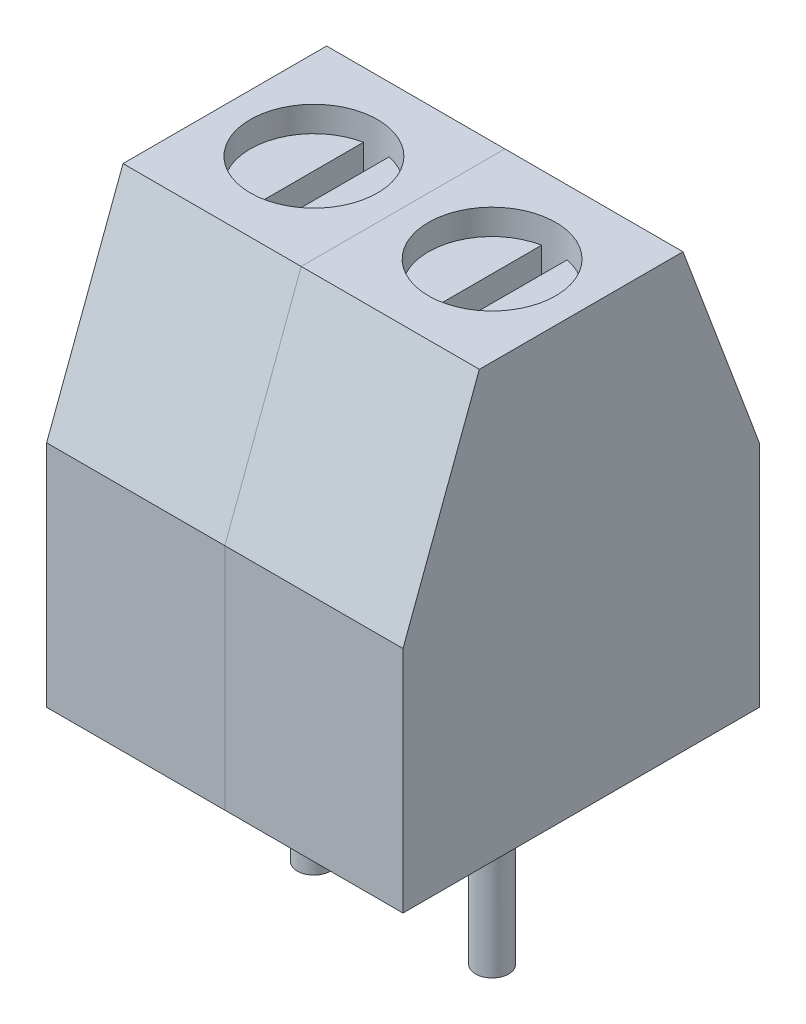
SolidWorks part; units mm, degrees
ref_plane "정면" through (0, 0, 0) normal (0, 0, 1) x (1, 0, 0)
ref_plane "윗면" through (0, 0, 0) normal (0, 1, 0) x (1, 0, 0)
ref_plane "우측면" through (0, 0, 0) normal (1, 0, 0) x (0, 0, -1)
sketch "스케치1" plane through (0, 0, 0) normal (1, 0, 0) x (0, 0, -1)
  line L0 (0, 4.5) -> (0, 8.5) construction
  line L1 (0, 0) -> (7, 0)
  line L2 (0, 0) -> (0, 4.5)
  line L3 (0, 8.5) -> (7, 8.5) construction
  line L4 (7, 0) -> (7, 4.5)
  line L5 (1.5, 8.5) -> (5.5, 8.5)
  line L6 (1.5, 8.5) -> (0, 4.5)
  line L7 (5.5, 8.5) -> (7, 4.5)
  line L8 (7, 4.5) -> (7, 8.5) construction
  line L9 (0, 4.5) -> (7, 4.5) construction
  point P10 (3.5, 8.5)
  dimension "D1" = 4
  dimension "D2" = 7
  dimension "D3" = 8.5
  dimension "D4" = 4.5
extrude "보스-돌출1" add sketch "스케치1" along normal blind 3.5
sketch "스케치3" plane through (0, 0, -7) normal (0, 0, -1) x (-1, 0, 0)
  line L0 (-3.5, 4.5) -> (0, 4.5) construction
  line L1 (-3.25, 0.5) -> (-0.25, 0.5)
  line L2 (-3.25, 0.5) -> (-3.25, 4.5)
  line L3 (-3.25, 4.5) -> (-0.25, 4.5)
  line L4 (-0.25, 0.5) -> (-0.25, 4.5)
  line L5 (-3.5, 0) -> (-3.5, 4.5) construction
  line L6 (0, 0) -> (0, 4.5) construction
  line L7 (-3.5, 0) -> (0, 0) construction
  dimension "D1" = 0.25
  dimension "D2" = 0.25
  dimension "D3" = 0.5
extrude "컷-돌출1" cut sketch "스케치3" against normal blind 1.5
sketch "스케치4" plane through (0, 8.5, 0) normal (0, 1, 0) x (1, 0, 0)
  circle A0 centre (1.75, 3.5) radius 1.25
extrude "컷-돌출2" cut sketch "스케치4" against normal blind 0.5
sketch "스케치5" plane through (0, 8, 0) normal (0, 1, 0) x (1, 0, 0)
  line L2 (1.5001, 4.7248) -> (1.5001, 2.2752)
  line L4 (1.9999, 4.7248) -> (1.9999, 2.2752)
  line L5 (1.5001, 4.7248) -> (1.9999, 2.2752) construction
  line L6 (1.5001, 2.2752) -> (1.9999, 4.7248) construction
  arc A0 (1.5001, 2.2752) -> (1.9999, 2.2752) centre (1.75, 3.5) ccw
  circle A1 centre (1.75, 3.5) radius 1.25
  arc A2 (1.9999, 4.7248) -> (1.5001, 4.7248) centre (1.75, 3.5) ccw
  dimension "D1" = 0
extrude "컷-돌출3" cut sketch "스케치5" against normal blind 0.5
sketch "스케치7" plane through (0, 0, -5.5) normal (0, 0, -1) x (-1, 0, 0)
  line L0 (-3.25, 4.5) -> (-3.25, 0.5) construction
  line L1 (-3.25, 0.5) -> (-0.25, 0.5) construction
  circle A0 centre (-1.75, 2) radius 1
  dimension "D1" = 1.5
  dimension "D2" = 2
  dimension "D3" = 1.5
extrude "컷-돌출4" cut sketch "스케치7" against normal blind 3
pattern_linear "선형 패턴1" [suppressed] count 3 spacing 3.5
sketch "Sketch1" plane through (0, 0, 0) normal (0, -1, 0) x (1, 0, 0)
  line L4 (0, 0) -> (0, -7)
  line L5 (0, -7) -> (3.5, -7)
  line L6 (3.5, -7) -> (3.5, 0)
  line L7 (3.5, 0) -> (0, 0)
  line L8 (0, 0) -> (0, -7)
  line L9 (0, -7) -> (3.5, -7)
  line L10 (3.5, -7) -> (3.5, 0)
  line L11 (3.5, 0) -> (0, 0)
  circle A0 centre (1.75, -3.5) radius 0.325
  dimension "D2" = 1.75
  dimension "D3" = 3.5
  dimension "D4" = 7
  dimension "D5" = 3.5
  dimension "D1" = 0
extrude "Boss-Extrude1" add sketch "Sketch1" along normal blind 3.5 contours A0
pattern_linear "LPattern1" count 2 spacing 3.5 along (1, 0, 0) of bodies 108
